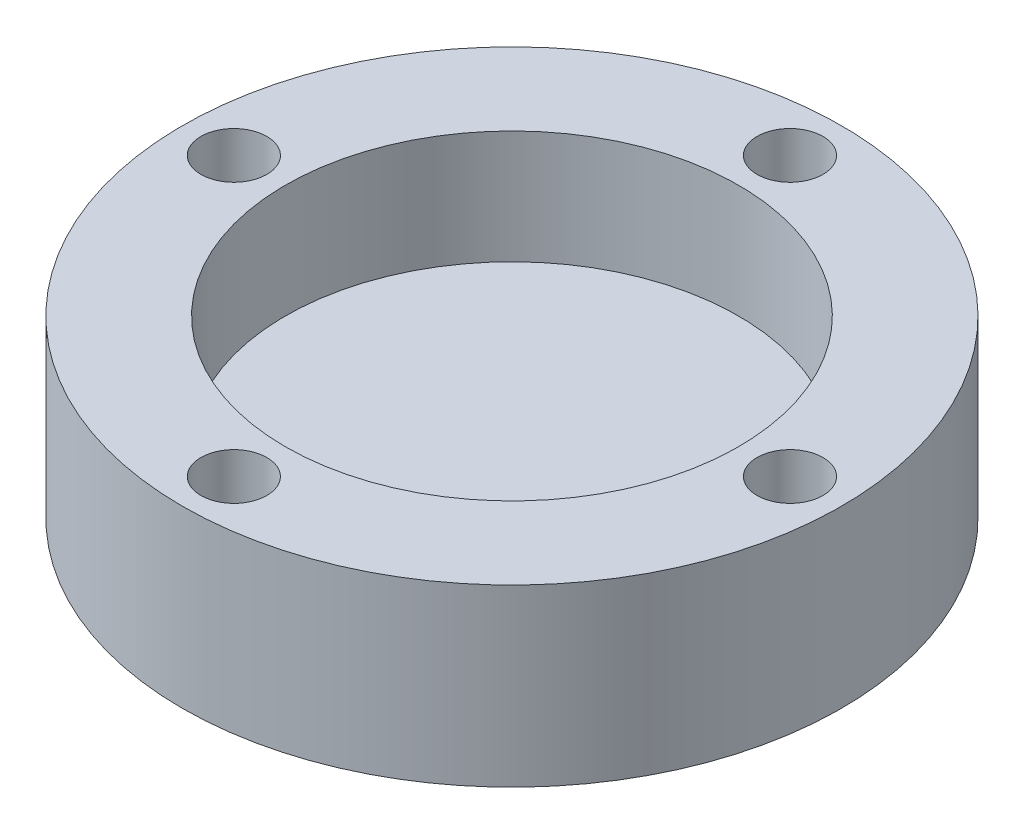
SolidWorks part; units mm, degrees
ref_plane "Front Plane" through (0, 0, 0) normal (0, 0, 1) x (1, 0, 0)
ref_plane "Top Plane" through (0, 0, 0) normal (0, 1, 0) x (1, 0, 0)
ref_plane "Right Plane" through (0, 0, 0) normal (1, 0, 0) x (0, 0, -1)
ref_axis "Axe1" through (0, 8.4, 0) along (0, -1, 0)
sketch "Esquisse1" plane through (0, 0, 0) normal (0, 0, 1) x (1, 0, 0)
  line L0 (11, 8.5) -> (11, 3)
  line L1 (11, 3) -> (0, 3)
  line L2 (0, 3) -> (0, 0)
  line L3 (0, 0) -> (16, 0)
  line L4 (16, 0) -> (16, 8.5)
  line L5 (11, 8.5) -> (16, 8.5)
  dimension "D1" = 5.5
  dimension "D2" = 3
  dimension "D3" = 11
  dimension "D4" = 5
revolve "MainRevolution" add sketch "Esquisse1" angle 360 about axis through (0, 8.4, 0) along (0, -1, 0)
sketch "Esquisse2" plane through (0, 8.5, 0) normal (0, 1, 0) x (1, 0, 0)
  circle A0 centre (13.5, 0) radius 1.6
  dimension "D1" = 3.2
  dimension "D2" = 13.5
extrude "FixingHole" cut sketch "Esquisse2" against normal through all
pattern_circular "FixingHoleRepetition" count 4 every 90 about axis through (0, 0, 0) along (0, 1, 0) of "FixingHole"
